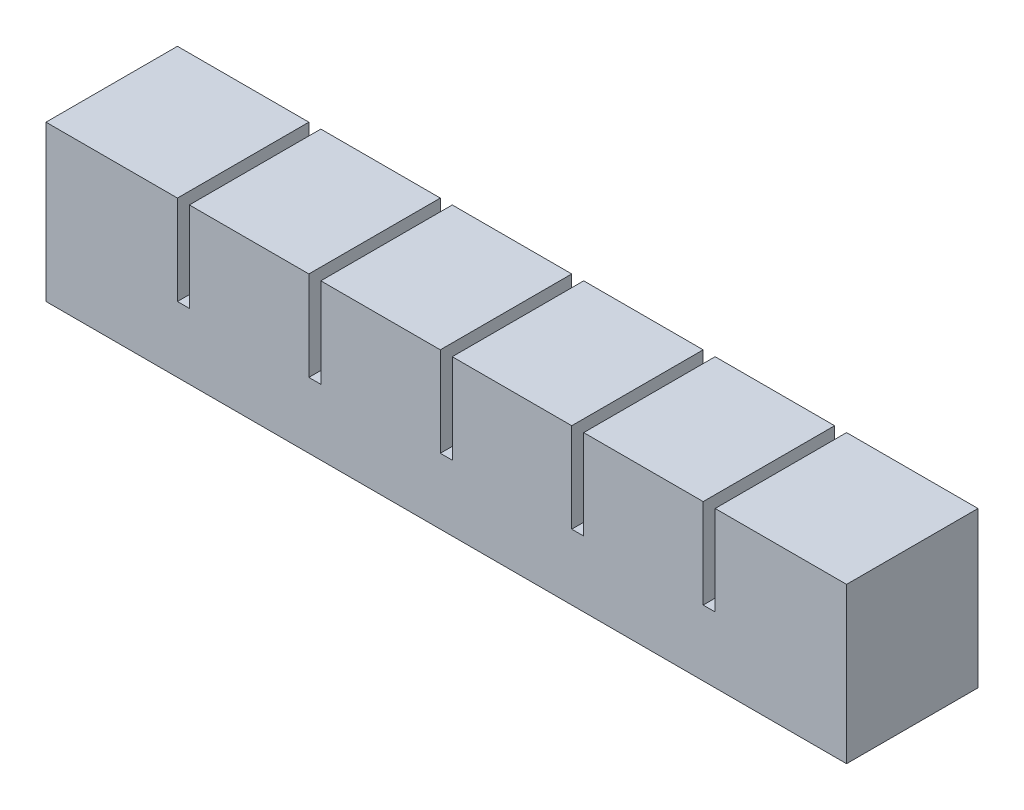
SolidWorks part; units mm, degrees
ref_plane "Front Plane" through (0, 0, 0) normal (0, 0, 1) x (1, 0, 0)
ref_plane "Top Plane" through (0, 0, 0) normal (0, 1, 0) x (1, 0, 0)
ref_plane "Right Plane" through (0, 0, 0) normal (1, 0, 0) x (0, 0, -1)
sketch "Sketch1" plane through (0, 0, 0) normal (0, 0, 1) x (1, 0, 0)
  line L1 (0, 0) -> (20, 0)
  line L2 (0, 0) -> (0, 20)
  line L3 (0, 20) -> (20, 20)
  line L4 (20, 0) -> (20, 20)
  dimension "D1" = 20
  dimension "D2" = 20
extrude "Boss-Extrude1" add sketch "Sketch1" along normal blind 22
sketch "Sketch2" plane through (0, 0, 0) normal (0, -1, 0) x (1, 0, 0)
  line L0 (20, 22) -> (20, 0) construction
  line L1 (4, 4) -> (16, 4)
  line L2 (4, 4) -> (4, 18)
  line L3 (4, 18) -> (16, 18)
  line L4 (16, 4) -> (16, 18)
  line L5 (0, 22) -> (20, 22) construction
  line L6 (0, 22) -> (0, 0) construction
  line L7 (0, 0) -> (20, 0) construction
  dimension "D1" = 4
  dimension "D2" = 4
  dimension "D3" = 4
  dimension "D4" = 4
extrude "Cut-Extrude1" cut sketch "Sketch2" against normal blind 16
sketch "Sketch3" plane through (20, 0, 0) normal (1, 0, 0) x (0, 0, -1)
  line L0 (0, 0) -> (0, 20) construction
  line L1 (-22, 0) -> (0, 0)
  line L2 (-22, 0) -> (-22, 5)
  line L3 (-22, 5) -> (0, 5)
  line L4 (0, 0) -> (0, 5)
  dimension "D1" = 5
extrude "Boss-Extrude2" add sketch "Sketch3" along normal blind 2
pattern_linear "LPattern1" count 6 spacing 22 along (1, 0, 0) of bodies 103
combine bodies "Combine1" operation type add bodies to combine 103 104 105 106 107 108
sketch "Sketch4" plane through (130, 0, 0) normal (1, 0, 0) x (0, 0, -1)
  line L1 (-22, 5) -> (0, 5)
  line L2 (-22, 5) -> (-22, 20)
  line L3 (-22, 20) -> (0, 20)
  line L4 (0, 5) -> (0, 20)
extrude "Boss-Extrude3" add sketch "Sketch4" along normal up to surface (2 mm away) up to face at (132, 2.5, 11)
sketch "Sketch5" plane through (0, 0, 0) normal (-1, 0, 0) x (0, 0, 1)
  line L1 (0, 20) -> (22, 20)
  line L2 (0, 20) -> (0, 0)
  line L3 (0, 0) -> (22, 0)
  line L4 (22, 20) -> (22, 0)
extrude "Boss-Extrude4" add sketch "Sketch5" along normal blind 2
ref_point "Point1"
sketch "Sketch6" plane through (0, 0, 0) normal (0, -1, 0) x (-1, 0, 0)
  line L0 (-126, -4) -> (-126, -18) construction
  line L1 (-4, -12) -> (-126, -12)
  line L2 (-4, -12) -> (-4, -10)
  line L3 (-4, -10) -> (-126, -10)
  line L4 (-126, -12) -> (-126, -10)
  line L5 (-4, -12) -> (-126, -10) construction
  line L6 (-4, -10) -> (-126, -12) construction
  point P0 (-65, -11)
  dimension "D1" = 2
extrude "Cut-Extrude2" cut sketch "Sketch6" against normal blind 2
sketch "Sketch7" plane through (0, 0, 0) normal (0, -1, 0) x (1, 0, 0)
  line L1 (-2, 22) -> (132, 22)
  line L2 (-2, 22) -> (-2, 0)
  line L3 (-2, 0) -> (132, 0)
  line L4 (132, 22) -> (132, 0)
extrude "Boss-Extrude5" add sketch "Sketch7" along normal blind 6
